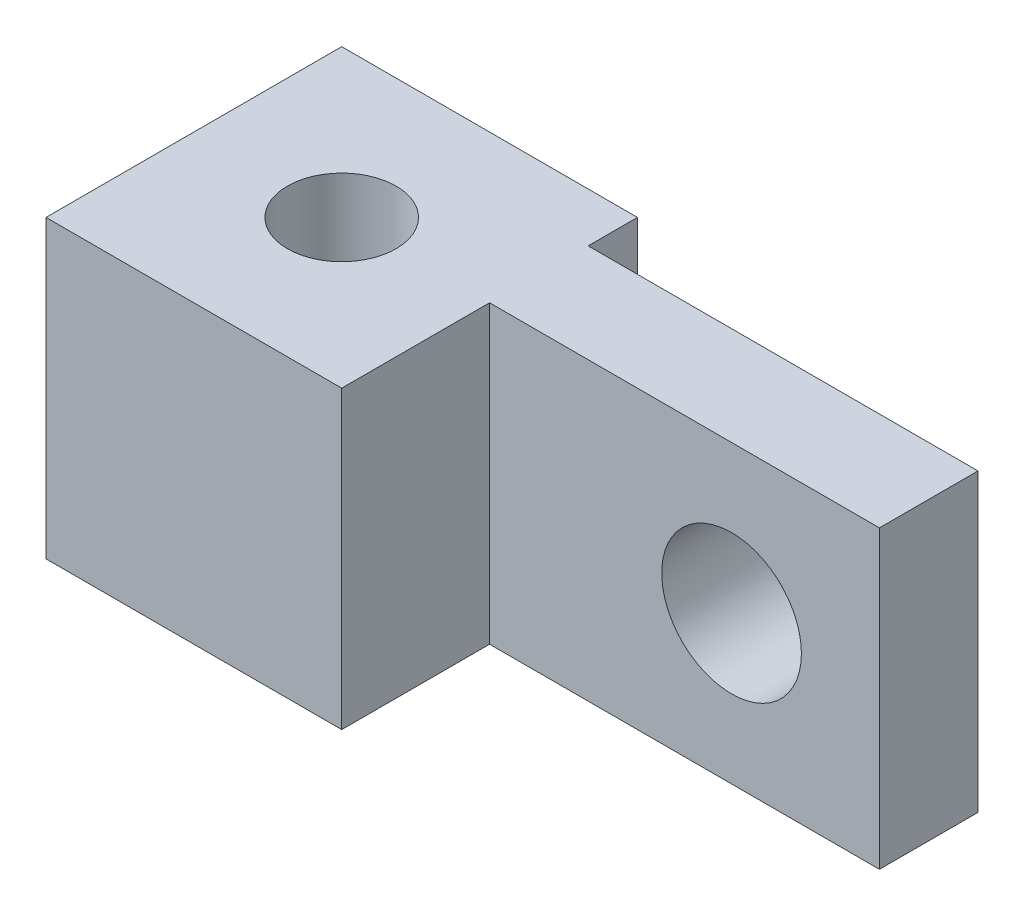
SolidWorks part; units mm, degrees
material "Copper"
ref_plane "Front" through (0, 0, 0) normal (0, 0, 1) x (1, 0, 0)
ref_plane "Top" through (0, 0, 0) normal (0, 1, 0) x (1, 0, 0)
ref_plane "Right" through (0, 0, 0) normal (1, 0, 0) x (0, 0, -1)
sketch "Sketch1" plane through (0, 0, 0) normal (0, 0, 1) x (1, 0, 0)
  line L0 (50.8, 204.55) -> (25.6875, 204.55) construction
  line L1 (25.6875, 204.55) -> (25.6875, 214.075) construction
  line L2 (50.8, 204.55) -> (25.6875, 204.55) construction
  line L3 (25.6875, 204.55) -> (25.6875, 214.075) construction
  line L5 (16.1625, 214.075) -> (60.325, 214.075)
  line L6 (16.1625, 214.075) -> (16.1625, 195.025)
  line L7 (16.1625, 195.025) -> (60.325, 195.025)
  line L8 (60.325, 214.075) -> (60.325, 195.025)
  point P7 (16.1625, 204.55)
  dimension "D1" = 9.525
  dimension "D2" = 9.525
extrude "Boss-Extrude1" add sketch "Sketch1" along normal blind 6.35
sketch "Sketch2" plane through (0, 0, 6.35) normal (0, 0, 1) x (1, 0, 0)
  line L0 (16.1625, 195.025) -> (60.325, 195.025) construction
  line L1 (16.1625, 214.075) -> (35.2125, 214.075)
  line L2 (16.1625, 214.075) -> (16.1625, 195.025)
  line L3 (16.1625, 195.025) -> (35.2125, 195.025)
  line L4 (35.2125, 214.075) -> (35.2125, 195.025)
  dimension "D1" = 19.05
extrude "Boss-Extrude2" add sketch "Sketch2" along normal mid plane 19.05
hole_wizard "M8x1.0 Tapped Hole1" positions "Sketch3" profile "Sketch4" tap size "M8x1.0" standard "ANSI Metric"
sketch "Sketch3" plane through (0, 214.075, 0) normal (0, 1, 0) x (1, 0, 0)
  line L0 (16.1625, 3.175) -> (35.2125, -15.875) construction
  point P0 (25.6875, -6.35)
  point P9 (0, 0)
  point P10 (0, 0)
  point P11 (16.1625, 3.175)
  point P14 (0, 0)
sketch "Sketch4" plane through (25.6875, 214.075, 6.35) normal (1, 0, 0) x (0, 0, 1)
  line L0 (0, 0) -> (0, 23.185)
  line L1 (0, 23.185) -> (3.5, 21.082)
  line L2 (3.5, 21.082) -> (3.5, 0)
  line L5 (3.5, 0) -> (0, 0)
  line L10 (0, 23.185) -> (-3.5, 21.082) construction
  line L11 (0, -6.35) -> (0, 107.95) construction
  dimension "Tap Drill Dia." = 7
  dimension "Tap Drill Depth" = 21.082
  dimension "Drill Angle" = 118
cosmetic thread "Hole Thread1" parameters "D1"=16.002, "D2"=8
hole_wizard "M8 Clearance Hole1" positions "Sketch5" profile "Sketch6" hole size "M8" standard "ANSI Metric"
sketch "Sketch5" plane through (0, 0, 6.35) normal (0, 0, 1) x (1, 0, 0)
  point P0 (50.8, 204.55)
  point P3 (0, 0)
sketch "Sketch6" plane through (50.8, 204.55, 6.35) normal (1, 0, 0) x (0, -1, 0)
  line L0 (0, 0) -> (0, 23.7859)
  line L1 (0, 23.7859) -> (4.5, 21.082)
  line L2 (4.5, 21.082) -> (4.5, 0)
  line L5 (4.5, 0) -> (0, 0)
  line L10 (0, 23.7859) -> (-4.5, 21.082) construction
  line L11 (0, -6.35) -> (0, 107.95) construction
  dimension "Hole Dia." = 9
  dimension "Hole Depth" = 21.082
  dimension "Drill Angle" = 118
